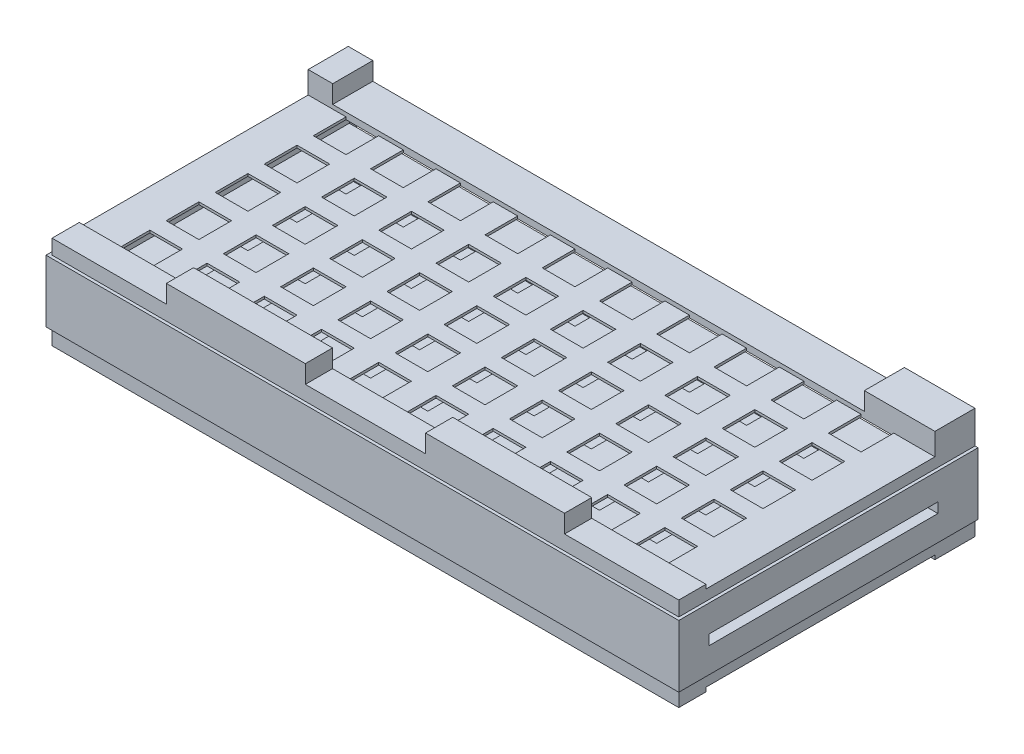
SolidWorks part; units mm, degrees
material "ABS"
ref_plane "Płaszczyzna przednia" through (0, 0, 0) normal (0, 0, 1) x (1, 0, 0)
ref_plane "Płaszczyzna górna" through (0, 0, 0) normal (0, 1, 0) x (1, 0, 0)
ref_plane "Płaszczyzna prawa" through (0, 0, 0) normal (1, 0, 0) x (0, 0, -1)
sketch "Szkic1" plane through (0, 0, 0) normal (0, 0, 1) x (1, 0, 0)
  line L15 (186, 34.1) -> (-188, 34.1)
  line L16 (186, 34.1) -> (186, -18.9)
  line L17 (186, -18.9) -> (-188, -18.9)
  line L18 (-188, 34.1) -> (-188, -18.9)
  point P0 (0, 0)
  dimension "D3" = 374
  dimension "D6" = 53
extrude "Dodanie-wyciągnięcie1" add sketch "Szkic1" along normal blind 177 contours L17 L18 L15 L16
sketch "Szkic5" plane through (0, -18.9, 0) normal (0, -1, 0) x (1, 0, 0)
  line L0 (186, 0) -> (-188, 0) construction
  line L1 (165.5, 48.5) -> (145.5, 48.5)
  line L2 (186, 177) -> (186, 0) construction
  line L3 (165.5, 48.5) -> (165.5, 68.5)
  line L4 (165.5, 68.5) -> (145.5, 68.5)
  line L5 (165.5, 18.5) -> (145.5, 18.5)
  line L6 (165.5, 18.5) -> (165.5, 38.5)
  line L7 (165.5, 38.5) -> (145.5, 38.5)
  line L8 (145.5, 18.5) -> (145.5, 38.5)
  line L9 (145.5, 48.5) -> (145.5, 68.5)
  line L10 (165.5, 78.5) -> (145.5, 78.5)
  line L11 (165.5, 78.5) -> (165.5, 98.5)
  line L12 (165.5, 98.5) -> (145.5, 98.5)
  line L13 (145.5, 78.5) -> (145.5, 98.5)
  line L14 (165.5, 108.5) -> (145.5, 108.5)
  line L15 (165.5, 108.5) -> (165.5, 128.5)
  line L16 (165.5, 128.5) -> (145.5, 128.5)
  line L17 (145.5, 108.5) -> (145.5, 128.5)
  line L18 (165.5, 138.5) -> (145.5, 138.5)
  line L19 (165.5, 138.5) -> (165.5, 158.5)
  line L20 (165.5, 158.5) -> (145.5, 158.5)
  line L21 (145.5, 138.5) -> (145.5, 158.5)
  line L22 (130.5, 48.5) -> (110.5, 48.5)
  line L23 (130.5, 48.5) -> (130.5, 68.5)
  line L24 (130.5, 68.5) -> (110.5, 68.5)
  line L25 (130.5, 18.5) -> (110.5, 18.5)
  line L26 (130.5, 18.5) -> (130.5, 38.5)
  line L27 (130.5, 38.5) -> (110.5, 38.5)
  line L28 (110.5, 18.5) -> (110.5, 38.5)
  line L29 (110.5, 48.5) -> (110.5, 68.5)
  line L30 (130.5, 78.5) -> (110.5, 78.5)
  line L31 (130.5, 78.5) -> (130.5, 98.5)
  line L32 (130.5, 98.5) -> (110.5, 98.5)
  line L33 (110.5, 78.5) -> (110.5, 98.5)
  line L34 (130.5, 108.5) -> (110.5, 108.5)
  line L35 (130.5, 108.5) -> (130.5, 128.5)
  line L36 (130.5, 128.5) -> (110.5, 128.5)
  line L37 (110.5, 108.5) -> (110.5, 128.5)
  line L38 (130.5, 138.5) -> (110.5, 138.5)
  line L39 (130.5, 138.5) -> (130.5, 158.5)
  line L40 (130.5, 158.5) -> (110.5, 158.5)
  line L41 (110.5, 138.5) -> (110.5, 158.5)
  line L42 (95.5, 48.5) -> (75.5, 48.5)
  line L43 (95.5, 48.5) -> (95.5, 68.5)
  line L44 (95.5, 68.5) -> (75.5, 68.5)
  line L45 (95.5, 18.5) -> (75.5, 18.5)
  line L46 (95.5, 18.5) -> (95.5, 38.5)
  line L47 (95.5, 38.5) -> (75.5, 38.5)
  line L48 (75.5, 18.5) -> (75.5, 38.5)
  line L49 (75.5, 48.5) -> (75.5, 68.5)
  line L50 (95.5, 78.5) -> (75.5, 78.5)
  line L51 (95.5, 78.5) -> (95.5, 98.5)
  line L52 (95.5, 98.5) -> (75.5, 98.5)
  line L53 (75.5, 78.5) -> (75.5, 98.5)
  line L54 (95.5, 108.5) -> (75.5, 108.5)
  line L55 (95.5, 108.5) -> (95.5, 128.5)
  line L56 (95.5, 128.5) -> (75.5, 128.5)
  line L57 (75.5, 108.5) -> (75.5, 128.5)
  line L58 (95.5, 138.5) -> (75.5, 138.5)
  line L59 (95.5, 138.5) -> (95.5, 158.5)
  line L60 (95.5, 158.5) -> (75.5, 158.5)
  line L61 (75.5, 138.5) -> (75.5, 158.5)
  line L62 (60.5, 48.5) -> (40.5, 48.5)
  line L63 (60.5, 48.5) -> (60.5, 68.5)
  line L64 (60.5, 68.5) -> (40.5, 68.5)
  line L65 (60.5, 18.5) -> (40.5, 18.5)
  line L66 (60.5, 18.5) -> (60.5, 38.5)
  line L67 (60.5, 38.5) -> (40.5, 38.5)
  line L68 (40.5, 18.5) -> (40.5, 38.5)
  line L69 (40.5, 48.5) -> (40.5, 68.5)
  line L70 (60.5, 78.5) -> (40.5, 78.5)
  line L71 (60.5, 78.5) -> (60.5, 98.5)
  line L72 (60.5, 98.5) -> (40.5, 98.5)
  line L73 (40.5, 78.5) -> (40.5, 98.5)
  line L74 (60.5, 108.5) -> (40.5, 108.5)
  line L75 (60.5, 108.5) -> (60.5, 128.5)
  line L76 (60.5, 128.5) -> (40.5, 128.5)
  line L77 (40.5, 108.5) -> (40.5, 128.5)
  line L78 (60.5, 138.5) -> (40.5, 138.5)
  line L79 (60.5, 138.5) -> (60.5, 158.5)
  line L80 (60.5, 158.5) -> (40.5, 158.5)
  line L81 (40.5, 138.5) -> (40.5, 158.5)
  line L82 (25.5, 48.5) -> (5.5, 48.5)
  line L83 (25.5, 48.5) -> (25.5, 68.5)
  line L84 (25.5, 68.5) -> (5.5, 68.5)
  line L85 (25.5, 18.5) -> (5.5, 18.5)
  line L86 (25.5, 18.5) -> (25.5, 38.5)
  line L87 (25.5, 38.5) -> (5.5, 38.5)
  line L88 (5.5, 18.5) -> (5.5, 38.5)
  line L89 (5.5, 48.5) -> (5.5, 68.5)
  line L90 (25.5, 78.5) -> (5.5, 78.5)
  line L91 (25.5, 78.5) -> (25.5, 98.5)
  line L92 (25.5, 98.5) -> (5.5, 98.5)
  line L93 (5.5, 78.5) -> (5.5, 98.5)
  line L94 (25.5, 108.5) -> (5.5, 108.5)
  line L95 (25.5, 108.5) -> (25.5, 128.5)
  line L96 (25.5, 128.5) -> (5.5, 128.5)
  line L97 (5.5, 108.5) -> (5.5, 128.5)
  line L98 (25.5, 138.5) -> (5.5, 138.5)
  line L99 (25.5, 138.5) -> (25.5, 158.5)
  line L100 (25.5, 158.5) -> (5.5, 158.5)
  line L101 (5.5, 138.5) -> (5.5, 158.5)
  line L102 (-9.5, 48.5) -> (-29.5, 48.5)
  line L103 (-9.5, 48.5) -> (-9.5, 68.5)
  line L104 (-9.5, 68.5) -> (-29.5, 68.5)
  line L105 (-9.5, 18.5) -> (-29.5, 18.5)
  line L106 (-9.5, 18.5) -> (-9.5, 38.5)
  line L107 (-9.5, 38.5) -> (-29.5, 38.5)
  line L108 (-29.5, 18.5) -> (-29.5, 38.5)
  line L109 (-29.5, 48.5) -> (-29.5, 68.5)
  line L110 (-9.5, 78.5) -> (-29.5, 78.5)
  line L111 (-9.5, 78.5) -> (-9.5, 98.5)
  line L112 (-9.5, 98.5) -> (-29.5, 98.5)
  line L113 (-29.5, 78.5) -> (-29.5, 98.5)
  line L114 (-9.5, 108.5) -> (-29.5, 108.5)
  line L115 (-9.5, 108.5) -> (-9.5, 128.5)
  line L116 (-9.5, 128.5) -> (-29.5, 128.5)
  line L117 (-29.5, 108.5) -> (-29.5, 128.5)
  line L118 (-9.5, 138.5) -> (-29.5, 138.5)
  line L119 (-9.5, 138.5) -> (-9.5, 158.5)
  line L120 (-9.5, 158.5) -> (-29.5, 158.5)
  line L121 (-29.5, 138.5) -> (-29.5, 158.5)
  line L122 (-44.5, 48.5) -> (-64.5, 48.5)
  line L123 (-44.5, 48.5) -> (-44.5, 68.5)
  line L124 (-44.5, 68.5) -> (-64.5, 68.5)
  line L125 (-44.5, 18.5) -> (-64.5, 18.5)
  line L126 (-44.5, 18.5) -> (-44.5, 38.5)
  line L127 (-44.5, 38.5) -> (-64.5, 38.5)
  line L128 (-64.5, 18.5) -> (-64.5, 38.5)
  line L129 (-64.5, 48.5) -> (-64.5, 68.5)
  line L130 (-44.5, 78.5) -> (-64.5, 78.5)
  line L131 (-44.5, 78.5) -> (-44.5, 98.5)
  line L132 (-44.5, 98.5) -> (-64.5, 98.5)
  line L133 (-64.5, 78.5) -> (-64.5, 98.5)
  line L134 (-44.5, 108.5) -> (-64.5, 108.5)
  line L135 (-44.5, 108.5) -> (-44.5, 128.5)
  line L136 (-44.5, 128.5) -> (-64.5, 128.5)
  line L137 (-64.5, 108.5) -> (-64.5, 128.5)
  line L138 (-44.5, 138.5) -> (-64.5, 138.5)
  line L139 (-44.5, 138.5) -> (-44.5, 158.5)
  line L140 (-44.5, 158.5) -> (-64.5, 158.5)
  line L141 (-64.5, 138.5) -> (-64.5, 158.5)
  line L142 (-79.5, 48.5) -> (-99.5, 48.5)
  line L143 (-79.5, 48.5) -> (-79.5, 68.5)
  line L144 (-79.5, 68.5) -> (-99.5, 68.5)
  line L145 (-79.5, 18.5) -> (-99.5, 18.5)
  line L146 (-79.5, 18.5) -> (-79.5, 38.5)
  line L147 (-79.5, 38.5) -> (-99.5, 38.5)
  line L148 (-99.5, 18.5) -> (-99.5, 38.5)
  line L149 (-99.5, 48.5) -> (-99.5, 68.5)
  line L150 (-79.5, 78.5) -> (-99.5, 78.5)
  line L151 (-79.5, 78.5) -> (-79.5, 98.5)
  line L152 (-79.5, 98.5) -> (-99.5, 98.5)
  line L153 (-99.5, 78.5) -> (-99.5, 98.5)
  line L154 (-79.5, 108.5) -> (-99.5, 108.5)
  line L155 (-79.5, 108.5) -> (-79.5, 128.5)
  line L156 (-79.5, 128.5) -> (-99.5, 128.5)
  line L157 (-99.5, 108.5) -> (-99.5, 128.5)
  line L158 (-79.5, 138.5) -> (-99.5, 138.5)
  line L159 (-79.5, 138.5) -> (-79.5, 158.5)
  line L160 (-79.5, 158.5) -> (-99.5, 158.5)
  line L161 (-99.5, 138.5) -> (-99.5, 158.5)
  line L162 (-114.5, 48.5) -> (-134.5, 48.5)
  line L163 (-114.5, 48.5) -> (-114.5, 68.5)
  line L164 (-114.5, 68.5) -> (-134.5, 68.5)
  line L165 (-114.5, 18.5) -> (-134.5, 18.5)
  line L166 (-114.5, 18.5) -> (-114.5, 38.5)
  line L167 (-114.5, 38.5) -> (-134.5, 38.5)
  line L168 (-134.5, 18.5) -> (-134.5, 38.5)
  line L169 (-134.5, 48.5) -> (-134.5, 68.5)
  line L170 (-114.5, 78.5) -> (-134.5, 78.5)
  line L171 (-114.5, 78.5) -> (-114.5, 98.5)
  line L172 (-114.5, 98.5) -> (-134.5, 98.5)
  line L173 (-134.5, 78.5) -> (-134.5, 98.5)
  line L174 (-114.5, 108.5) -> (-134.5, 108.5)
  line L175 (-114.5, 108.5) -> (-114.5, 128.5)
  line L176 (-114.5, 128.5) -> (-134.5, 128.5)
  line L177 (-134.5, 108.5) -> (-134.5, 128.5)
  line L178 (-114.5, 138.5) -> (-134.5, 138.5)
  line L179 (-114.5, 138.5) -> (-114.5, 158.5)
  line L180 (-114.5, 158.5) -> (-134.5, 158.5)
  line L181 (-134.5, 138.5) -> (-134.5, 158.5)
  line L182 (-149.5, 48.5) -> (-169.5, 48.5)
  line L183 (-149.5, 48.5) -> (-149.5, 68.5)
  line L184 (-149.5, 68.5) -> (-169.5, 68.5)
  line L185 (-149.5, 18.5) -> (-169.5, 18.5)
  line L186 (-149.5, 18.5) -> (-149.5, 38.5)
  line L187 (-149.5, 38.5) -> (-169.5, 38.5)
  line L188 (-169.5, 18.5) -> (-169.5, 38.5)
  line L189 (-169.5, 48.5) -> (-169.5, 68.5)
  line L190 (-149.5, 78.5) -> (-169.5, 78.5)
  line L191 (-149.5, 78.5) -> (-149.5, 98.5)
  line L192 (-149.5, 98.5) -> (-169.5, 98.5)
  line L193 (-169.5, 78.5) -> (-169.5, 98.5)
  line L194 (-149.5, 108.5) -> (-169.5, 108.5)
  line L195 (-149.5, 108.5) -> (-149.5, 128.5)
  line L196 (-149.5, 128.5) -> (-169.5, 128.5)
  line L197 (-169.5, 108.5) -> (-169.5, 128.5)
  line L198 (-149.5, 138.5) -> (-169.5, 138.5)
  line L199 (-149.5, 138.5) -> (-149.5, 158.5)
  line L200 (-149.5, 158.5) -> (-169.5, 158.5)
  line L201 (-169.5, 138.5) -> (-169.5, 158.5)
  line L202 (186, 177) -> (-188, 177) construction
  line L203 (-188, 177) -> (-188, 0) construction
  dimension "D1" = 18.5
  dimension "D2" = 20.5
  dimension "D3" = 20
  dimension "D4" = 20
  dimension "D7" = 20
  dimension "D8" = 20
  dimension "D9" = 15
  dimension "D10" = 18.5
  dimension "D11" = 18.5
  dimension "D5" = 5
  dimension "D6" = 10
extrude "Wytnij-wyciągnięcie4" cut sketch "Szkic5" against normal blind 104
sketch "Szkic7" plane through (0, 0, 0) normal (0, 0, -1) x (-1, 0, 0)
  line L5 (-186, -18.9) -> (188, -18.9) construction
  line L7 (-184, 32.1) -> (186, 32.1)
  line L8 (-184, 32.1) -> (-184, 12.7)
  line L9 (-184, 12.7) -> (186, 12.7)
  line L10 (186, 32.1) -> (186, 12.7)
  line L12 (-186, 34.1) -> (-186, -18.9) construction
  line L13 (-184, -16.9) -> (186, -16.9)
  line L14 (-184, -16.9) -> (-184, 2.5)
  line L15 (-184, 2.5) -> (186, 2.5)
  line L16 (186, -16.9) -> (186, 2.5)
  line L17 (-186, 34.1) -> (188, 34.1) construction
  dimension "D1" = 370
  dimension "D2" = 2
  dimension "D3" = 2
  dimension "D4" = 2
  dimension "D5" = 2
  dimension "D6" = 370
  dimension "D7" = 370
  dimension "D8" = 19.4
  dimension "D9" = 19.4
extrude "Wytnij-wyciągnięcie5" cut sketch "Szkic7" against normal blind 175
sketch "Szkic9" plane through (186, 0, 0) normal (1, 0, 0) x (0, 0, -1)
  line L15 (-158.5, 10.7) -> (-158.5, 4.5)
  line L17 (-18.5, 10.7) -> (-158.5, 10.7)
  line L18 (-18.5, 10.7) -> (-18.5, 4.5)
  line L19 (-18.5, 4.5) -> (-158.5, 4.5)
extrude "Wytnij-wyciągnięcie6" cut sketch "Szkic9" against normal blind 374
sketch "Szkic15" plane through (0, 34.1, 0) normal (0, 1, 0) x (1, 0, 0)
  line L1 (-188, 0) -> (186, 0)
  line L2 (-188, 0) -> (-188, -177)
  line L3 (-188, -177) -> (186, -177)
  line L4 (186, 0) -> (186, -177)
  line L5 (-169.5, -18.5) -> (-149.5, -18.5)
  line L6 (-169.5, -18.5) -> (-169.5, -38.5)
  line L7 (-169.5, -38.5) -> (-149.5, -38.5)
  line L8 (-149.5, -18.5) -> (-149.5, -38.5)
  line L9 (-134.5, -18.5) -> (-114.5, -18.5)
  line L10 (-134.5, -18.5) -> (-134.5, -38.5)
  line L11 (-134.5, -38.5) -> (-114.5, -38.5)
  line L12 (-114.5, -18.5) -> (-114.5, -38.5)
  line L13 (-99.5, -18.5) -> (-79.5, -18.5)
  line L14 (-99.5, -18.5) -> (-99.5, -38.5)
  line L15 (-99.5, -38.5) -> (-79.5, -38.5)
  line L16 (-79.5, -18.5) -> (-79.5, -38.5)
  line L17 (-64.5, -18.5) -> (-44.5, -18.5)
  line L18 (-64.5, -18.5) -> (-64.5, -38.5)
  line L19 (-64.5, -38.5) -> (-44.5, -38.5)
  line L20 (-44.5, -18.5) -> (-44.5, -38.5)
  line L21 (-29.5, -18.5) -> (-9.5, -18.5)
  line L22 (-29.5, -18.5) -> (-29.5, -38.5)
  line L23 (-29.5, -38.5) -> (-9.5, -38.5)
  line L24 (-9.5, -18.5) -> (-9.5, -38.5)
  line L25 (5.5, -18.5) -> (25.5, -18.5)
  line L26 (5.5, -18.5) -> (5.5, -38.5)
  line L27 (5.5, -38.5) -> (25.5, -38.5)
  line L28 (25.5, -18.5) -> (25.5, -38.5)
  line L29 (40.5, -18.5) -> (60.5, -18.5)
  line L30 (40.5, -18.5) -> (40.5, -38.5)
  line L31 (40.5, -38.5) -> (60.5, -38.5)
  line L32 (60.5, -18.5) -> (60.5, -38.5)
  line L33 (75.5, -18.5) -> (95.5, -18.5)
  line L34 (75.5, -18.5) -> (75.5, -38.5)
  line L35 (75.5, -38.5) -> (95.5, -38.5)
  line L36 (95.5, -18.5) -> (95.5, -38.5)
  line L37 (110.5, -18.5) -> (130.5, -18.5)
  line L38 (110.5, -18.5) -> (110.5, -38.5)
  line L39 (110.5, -38.5) -> (130.5, -38.5)
  line L40 (130.5, -18.5) -> (130.5, -38.5)
  line L41 (145.5, -18.5) -> (165.5, -18.5)
  line L42 (145.5, -18.5) -> (145.5, -38.5)
  line L43 (145.5, -38.5) -> (165.5, -38.5)
  line L44 (165.5, -18.5) -> (165.5, -38.5)
  line L45 (145.5, -48.5) -> (165.5, -48.5)
  line L46 (145.5, -48.5) -> (145.5, -68.5)
  line L47 (145.5, -68.5) -> (165.5, -68.5)
  line L48 (165.5, -48.5) -> (165.5, -68.5)
  line L49 (145.5, -78.5) -> (165.5, -78.5)
  line L50 (145.5, -78.5) -> (145.5, -98.5)
  line L51 (145.5, -98.5) -> (165.5, -98.5)
  line L52 (165.5, -78.5) -> (165.5, -98.5)
  line L53 (145.5, -108.5) -> (165.5, -108.5)
  line L54 (145.5, -108.5) -> (145.5, -128.5)
  line L55 (145.5, -128.5) -> (165.5, -128.5)
  line L56 (165.5, -108.5) -> (165.5, -128.5)
  line L57 (145.5, -138.5) -> (165.5, -138.5)
  line L58 (145.5, -138.5) -> (145.5, -158.5)
  line L59 (145.5, -158.5) -> (165.5, -158.5)
  line L60 (165.5, -138.5) -> (165.5, -158.5)
  line L61 (110.5, -48.5) -> (130.5, -48.5)
  line L62 (110.5, -48.5) -> (110.5, -68.5)
  line L63 (110.5, -68.5) -> (130.5, -68.5)
  line L64 (130.5, -48.5) -> (130.5, -68.5)
  line L65 (110.5, -78.5) -> (130.5, -78.5)
  line L66 (110.5, -78.5) -> (110.5, -98.5)
  line L67 (110.5, -98.5) -> (130.5, -98.5)
  line L68 (130.5, -78.5) -> (130.5, -98.5)
  line L69 (110.5, -108.5) -> (130.5, -108.5)
  line L70 (110.5, -108.5) -> (110.5, -128.5)
  line L71 (110.5, -128.5) -> (130.5, -128.5)
  line L72 (130.5, -108.5) -> (130.5, -128.5)
  line L73 (110.5, -138.5) -> (130.5, -138.5)
  line L74 (110.5, -138.5) -> (110.5, -158.5)
  line L75 (110.5, -158.5) -> (130.5, -158.5)
  line L76 (130.5, -138.5) -> (130.5, -158.5)
  line L77 (75.5, -48.5) -> (95.5, -48.5)
  line L78 (75.5, -48.5) -> (75.5, -68.5)
  line L79 (75.5, -68.5) -> (95.5, -68.5)
  line L80 (95.5, -48.5) -> (95.5, -68.5)
  line L81 (75.5, -78.5) -> (95.5, -78.5)
  line L82 (75.5, -78.5) -> (75.5, -98.5)
  line L83 (75.5, -98.5) -> (95.5, -98.5)
  line L84 (95.5, -78.5) -> (95.5, -98.5)
  line L85 (75.5, -108.5) -> (95.5, -108.5)
  line L86 (75.5, -108.5) -> (75.5, -128.5)
  line L87 (75.5, -128.5) -> (95.5, -128.5)
  line L88 (95.5, -108.5) -> (95.5, -128.5)
  line L89 (75.5, -138.5) -> (95.5, -138.5)
  line L90 (75.5, -138.5) -> (75.5, -158.5)
  line L91 (75.5, -158.5) -> (95.5, -158.5)
  line L92 (95.5, -138.5) -> (95.5, -158.5)
  line L93 (40.5, -48.5) -> (60.5, -48.5)
  line L94 (40.5, -48.5) -> (40.5, -68.5)
  line L95 (40.5, -68.5) -> (60.5, -68.5)
  line L96 (60.5, -48.5) -> (60.5, -68.5)
  line L97 (40.5, -78.5) -> (60.5, -78.5)
  line L98 (40.5, -78.5) -> (40.5, -98.5)
  line L99 (40.5, -98.5) -> (60.5, -98.5)
  line L100 (60.5, -78.5) -> (60.5, -98.5)
  line L101 (40.5, -108.5) -> (60.5, -108.5)
  line L102 (40.5, -108.5) -> (40.5, -128.5)
  line L103 (40.5, -128.5) -> (60.5, -128.5)
  line L104 (60.5, -108.5) -> (60.5, -128.5)
  line L105 (5.5, -48.5) -> (25.5, -48.5)
  line L106 (5.5, -48.5) -> (5.5, -68.5)
  line L107 (5.5, -68.5) -> (25.5, -68.5)
  line L108 (25.5, -48.5) -> (25.5, -68.5)
  line L109 (5.5, -78.5) -> (25.5, -78.5)
  line L110 (5.5, -78.5) -> (5.5, -98.5)
  line L111 (5.5, -98.5) -> (25.5, -98.5)
  line L112 (25.5, -78.5) -> (25.5, -98.5)
  line L113 (5.5, -108.5) -> (25.5, -108.5)
  line L114 (5.5, -108.5) -> (5.5, -128.5)
  line L115 (5.5, -128.5) -> (25.5, -128.5)
  line L116 (25.5, -108.5) -> (25.5, -128.5)
  line L117 (5.5, -138.5) -> (25.5, -138.5)
  line L118 (5.5, -138.5) -> (5.5, -158.5)
  line L119 (5.5, -158.5) -> (25.5, -158.5)
  line L120 (25.5, -138.5) -> (25.5, -158.5)
  line L121 (40.5, -138.5) -> (60.5, -138.5)
  line L122 (40.5, -138.5) -> (40.5, -158.5)
  line L123 (40.5, -158.5) -> (60.5, -158.5)
  line L124 (60.5, -138.5) -> (60.5, -158.5)
  line L125 (-29.5, -48.5) -> (-9.5, -48.5)
  line L126 (-29.5, -48.5) -> (-29.5, -68.5)
  line L127 (-29.5, -68.5) -> (-9.5, -68.5)
  line L128 (-9.5, -48.5) -> (-9.5, -68.5)
  line L129 (-29.5, -78.5) -> (-9.5, -78.5)
  line L130 (-29.5, -78.5) -> (-29.5, -98.5)
  line L131 (-29.5, -98.5) -> (-9.5, -98.5)
  line L132 (-9.5, -78.5) -> (-9.5, -98.5)
  line L133 (-29.5, -108.5) -> (-9.5, -108.5)
  line L134 (-29.5, -108.5) -> (-29.5, -128.5)
  line L135 (-29.5, -128.5) -> (-9.5, -128.5)
  line L136 (-9.5, -108.5) -> (-9.5, -128.5)
  line L137 (-29.5, -138.5) -> (-9.5, -138.5)
  line L138 (-29.5, -138.5) -> (-29.5, -158.5)
  line L139 (-29.5, -158.5) -> (-9.5, -158.5)
  line L140 (-9.5, -138.5) -> (-9.5, -158.5)
  line L141 (-64.5, -48.5) -> (-44.5, -48.5)
  line L142 (-64.5, -48.5) -> (-64.5, -68.5)
  line L143 (-64.5, -68.5) -> (-44.5, -68.5)
  line L144 (-44.5, -48.5) -> (-44.5, -68.5)
  line L145 (-64.5, -78.5) -> (-44.5, -78.5)
  line L146 (-64.5, -78.5) -> (-64.5, -98.5)
  line L147 (-64.5, -98.5) -> (-44.5, -98.5)
  line L148 (-44.5, -78.5) -> (-44.5, -98.5)
  line L149 (-64.5, -108.5) -> (-44.5, -108.5)
  line L150 (-64.5, -108.5) -> (-64.5, -128.5)
  line L151 (-64.5, -128.5) -> (-44.5, -128.5)
  line L152 (-44.5, -108.5) -> (-44.5, -128.5)
  line L153 (-64.5, -138.5) -> (-44.5, -138.5)
  line L154 (-64.5, -138.5) -> (-64.5, -158.5)
  line L155 (-64.5, -158.5) -> (-44.5, -158.5)
  line L156 (-44.5, -138.5) -> (-44.5, -158.5)
  line L157 (-99.5, -48.5) -> (-79.5, -48.5)
  line L158 (-99.5, -48.5) -> (-99.5, -68.5)
  line L159 (-99.5, -68.5) -> (-79.5, -68.5)
  line L160 (-79.5, -48.5) -> (-79.5, -68.5)
  line L161 (-99.5, -78.5) -> (-79.5, -78.5)
  line L162 (-99.5, -78.5) -> (-99.5, -98.5)
  line L163 (-99.5, -98.5) -> (-79.5, -98.5)
  line L164 (-79.5, -78.5) -> (-79.5, -98.5)
  line L165 (-99.5, -108.5) -> (-79.5, -108.5)
  line L166 (-99.5, -108.5) -> (-99.5, -128.5)
  line L167 (-99.5, -128.5) -> (-79.5, -128.5)
  line L168 (-79.5, -108.5) -> (-79.5, -128.5)
  line L169 (-99.5, -138.5) -> (-79.5, -138.5)
  line L170 (-99.5, -138.5) -> (-99.5, -158.5)
  line L171 (-99.5, -158.5) -> (-79.5, -158.5)
  line L172 (-79.5, -138.5) -> (-79.5, -158.5)
  line L173 (-134.5, -48.5) -> (-114.5, -48.5)
  line L174 (-134.5, -48.5) -> (-134.5, -68.5)
  line L175 (-134.5, -68.5) -> (-114.5, -68.5)
  line L176 (-114.5, -48.5) -> (-114.5, -68.5)
  line L177 (-134.5, -78.5) -> (-114.5, -78.5)
  line L178 (-134.5, -78.5) -> (-134.5, -98.5)
  line L179 (-134.5, -98.5) -> (-114.5, -98.5)
  line L180 (-114.5, -78.5) -> (-114.5, -98.5)
  line L181 (-134.5, -108.5) -> (-114.5, -108.5)
  line L182 (-134.5, -108.5) -> (-134.5, -128.5)
  line L183 (-134.5, -128.5) -> (-114.5, -128.5)
  line L184 (-114.5, -108.5) -> (-114.5, -128.5)
  line L185 (-134.5, -138.5) -> (-114.5, -138.5)
  line L186 (-134.5, -138.5) -> (-134.5, -158.5)
  line L187 (-134.5, -158.5) -> (-114.5, -158.5)
  line L188 (-114.5, -138.5) -> (-114.5, -158.5)
  line L189 (-169.5, -48.5) -> (-149.5, -48.5)
  line L190 (-169.5, -48.5) -> (-169.5, -68.5)
  line L191 (-169.5, -68.5) -> (-149.5, -68.5)
  line L192 (-149.5, -48.5) -> (-149.5, -68.5)
  line L193 (-169.5, -78.5) -> (-149.5, -78.5)
  line L194 (-169.5, -78.5) -> (-169.5, -98.5)
  line L195 (-169.5, -98.5) -> (-149.5, -98.5)
  line L196 (-149.5, -78.5) -> (-149.5, -98.5)
  line L197 (-169.5, -108.5) -> (-149.5, -108.5)
  line L198 (-169.5, -108.5) -> (-169.5, -128.5)
  line L199 (-169.5, -128.5) -> (-149.5, -128.5)
  line L200 (-149.5, -108.5) -> (-149.5, -128.5)
  line L201 (-169.5, -138.5) -> (-149.5, -138.5)
  line L202 (-169.5, -138.5) -> (-169.5, -158.5)
  line L203 (-169.5, -158.5) -> (-149.5, -158.5)
  line L204 (-149.5, -138.5) -> (-149.5, -158.5)
extrude "Dodanie-wyciągnięcie6" add sketch "Szkic15" along normal blind 1
sketch "Szkic16" plane through (0, -18.9, 0) normal (0, -1, 0) x (1, 0, 0)
  line L1 (186, 0) -> (-188, 0)
  line L2 (186, 0) -> (186, 177)
  line L3 (186, 177) -> (-188, 177)
  line L4 (-188, 0) -> (-188, 177)
  line L5 (165.5, 18.5) -> (145.5, 18.5)
  line L6 (165.5, 18.5) -> (165.5, 38.5)
  line L7 (165.5, 38.5) -> (145.5, 38.5)
  line L8 (145.5, 18.5) -> (145.5, 38.5)
  line L9 (130.5, 18.5) -> (110.5, 18.5)
  line L10 (130.5, 18.5) -> (130.5, 38.5)
  line L11 (130.5, 38.5) -> (110.5, 38.5)
  line L12 (110.5, 18.5) -> (110.5, 38.5)
  line L13 (95.5, 18.5) -> (75.5, 18.5)
  line L14 (95.5, 18.5) -> (95.5, 38.5)
  line L15 (95.5, 38.5) -> (75.5, 38.5)
  line L16 (75.5, 18.5) -> (75.5, 38.5)
  line L17 (60.5, 18.5) -> (40.5, 18.5)
  line L18 (60.5, 18.5) -> (60.5, 38.5)
  line L19 (60.5, 38.5) -> (40.5, 38.5)
  line L20 (40.5, 18.5) -> (40.5, 38.5)
  line L21 (25.5, 18.5) -> (5.5, 18.5)
  line L22 (25.5, 18.5) -> (25.5, 38.5)
  line L23 (25.5, 38.5) -> (5.5, 38.5)
  line L24 (5.5, 18.5) -> (5.5, 38.5)
  line L25 (-9.5, 18.5) -> (-29.5, 18.5)
  line L26 (-9.5, 18.5) -> (-9.5, 38.5)
  line L27 (-9.5, 38.5) -> (-29.5, 38.5)
  line L28 (-29.5, 18.5) -> (-29.5, 38.5)
  line L29 (-44.5, 18.5) -> (-64.5, 18.5)
  line L30 (-44.5, 18.5) -> (-44.5, 38.5)
  line L31 (-44.5, 38.5) -> (-64.5, 38.5)
  line L32 (-64.5, 18.5) -> (-64.5, 38.5)
  line L33 (-79.5, 18.5) -> (-99.5, 18.5)
  line L34 (-79.5, 18.5) -> (-79.5, 38.5)
  line L35 (-79.5, 38.5) -> (-99.5, 38.5)
  line L36 (-99.5, 18.5) -> (-99.5, 38.5)
  line L37 (-114.5, 18.5) -> (-134.5, 18.5)
  line L38 (-114.5, 18.5) -> (-114.5, 38.5)
  line L39 (-114.5, 38.5) -> (-134.5, 38.5)
  line L40 (-134.5, 18.5) -> (-134.5, 38.5)
  line L41 (-149.5, 18.5) -> (-169.5, 18.5)
  line L42 (-149.5, 18.5) -> (-149.5, 38.5)
  line L43 (-149.5, 38.5) -> (-169.5, 38.5)
  line L44 (-169.5, 18.5) -> (-169.5, 38.5)
  line L45 (165.5, 48.5) -> (145.5, 48.5)
  line L46 (165.5, 48.5) -> (165.5, 68.5)
  line L47 (165.5, 68.5) -> (145.5, 68.5)
  line L48 (145.5, 48.5) -> (145.5, 68.5)
  line L49 (130.5, 48.5) -> (110.5, 48.5)
  line L50 (130.5, 48.5) -> (130.5, 68.5)
  line L51 (130.5, 68.5) -> (110.5, 68.5)
  line L52 (110.5, 48.5) -> (110.5, 68.5)
  line L53 (95.5, 48.5) -> (75.5, 48.5)
  line L54 (95.5, 48.5) -> (95.5, 68.5)
  line L55 (95.5, 68.5) -> (75.5, 68.5)
  line L56 (75.5, 48.5) -> (75.5, 68.5)
  line L57 (60.5, 48.5) -> (40.5, 48.5)
  line L58 (60.5, 48.5) -> (60.5, 68.5)
  line L59 (60.5, 68.5) -> (40.5, 68.5)
  line L60 (40.5, 48.5) -> (40.5, 68.5)
  line L61 (25.5, 48.5) -> (5.5, 48.5)
  line L62 (25.5, 48.5) -> (25.5, 68.5)
  line L63 (25.5, 68.5) -> (5.5, 68.5)
  line L64 (5.5, 48.5) -> (5.5, 68.5)
  line L65 (-9.5, 48.5) -> (-29.5, 48.5)
  line L66 (-9.5, 48.5) -> (-9.5, 68.5)
  line L67 (-9.5, 68.5) -> (-29.5, 68.5)
  line L68 (-29.5, 48.5) -> (-29.5, 68.5)
  line L69 (-44.5, 48.5) -> (-64.5, 48.5)
  line L70 (-44.5, 48.5) -> (-44.5, 68.5)
  line L71 (-44.5, 68.5) -> (-64.5, 68.5)
  line L72 (-64.5, 48.5) -> (-64.5, 68.5)
  line L73 (-79.5, 48.5) -> (-99.5, 48.5)
  line L74 (-79.5, 48.5) -> (-79.5, 68.5)
  line L75 (-79.5, 68.5) -> (-99.5, 68.5)
  line L76 (-99.5, 48.5) -> (-99.5, 68.5)
  line L77 (-114.5, 48.5) -> (-134.5, 48.5)
  line L78 (-114.5, 48.5) -> (-114.5, 68.5)
  line L79 (-114.5, 68.5) -> (-134.5, 68.5)
  line L80 (-134.5, 48.5) -> (-134.5, 68.5)
  line L81 (-149.5, 48.5) -> (-169.5, 48.5)
  line L82 (-149.5, 48.5) -> (-149.5, 68.5)
  line L83 (-149.5, 68.5) -> (-169.5, 68.5)
  line L84 (-169.5, 48.5) -> (-169.5, 68.5)
  line L85 (-149.5, 78.5) -> (-169.5, 78.5)
  line L86 (-149.5, 78.5) -> (-149.5, 98.5)
  line L87 (-149.5, 98.5) -> (-169.5, 98.5)
  line L88 (-169.5, 78.5) -> (-169.5, 98.5)
  line L89 (-149.5, 108.5) -> (-169.5, 108.5)
  line L90 (-149.5, 108.5) -> (-149.5, 128.5)
  line L91 (-149.5, 128.5) -> (-169.5, 128.5)
  line L92 (-169.5, 108.5) -> (-169.5, 128.5)
  line L93 (-149.5, 138.5) -> (-169.5, 138.5)
  line L94 (-149.5, 138.5) -> (-149.5, 158.5)
  line L95 (-149.5, 158.5) -> (-169.5, 158.5)
  line L96 (-169.5, 138.5) -> (-169.5, 158.5)
  line L97 (-114.5, 78.5) -> (-134.5, 78.5)
  line L98 (-114.5, 78.5) -> (-114.5, 98.5)
  line L99 (-114.5, 98.5) -> (-134.5, 98.5)
  line L100 (-134.5, 78.5) -> (-134.5, 98.5)
  line L101 (-114.5, 108.5) -> (-134.5, 108.5)
  line L102 (-114.5, 108.5) -> (-114.5, 128.5)
  line L103 (-114.5, 128.5) -> (-134.5, 128.5)
  line L104 (-134.5, 108.5) -> (-134.5, 128.5)
  line L105 (-114.5, 138.5) -> (-134.5, 138.5)
  line L106 (-114.5, 138.5) -> (-114.5, 158.5)
  line L107 (-114.5, 158.5) -> (-134.5, 158.5)
  line L108 (-134.5, 138.5) -> (-134.5, 158.5)
  line L109 (-79.5, 78.5) -> (-99.5, 78.5)
  line L110 (-79.5, 78.5) -> (-79.5, 98.5)
  line L111 (-79.5, 98.5) -> (-99.5, 98.5)
  line L112 (-99.5, 78.5) -> (-99.5, 98.5)
  line L113 (-79.5, 108.5) -> (-99.5, 108.5)
  line L114 (-79.5, 108.5) -> (-79.5, 128.5)
  line L115 (-79.5, 128.5) -> (-99.5, 128.5)
  line L116 (-99.5, 108.5) -> (-99.5, 128.5)
  line L117 (-79.5, 138.5) -> (-99.5, 138.5)
  line L118 (-79.5, 138.5) -> (-79.5, 158.5)
  line L119 (-79.5, 158.5) -> (-99.5, 158.5)
  line L120 (-99.5, 138.5) -> (-99.5, 158.5)
  line L121 (-44.5, 78.5) -> (-64.5, 78.5)
  line L122 (-44.5, 78.5) -> (-44.5, 98.5)
  line L123 (-44.5, 98.5) -> (-64.5, 98.5)
  line L124 (-64.5, 78.5) -> (-64.5, 98.5)
  line L125 (-44.5, 108.5) -> (-64.5, 108.5)
  line L126 (-44.5, 108.5) -> (-44.5, 128.5)
  line L127 (-44.5, 128.5) -> (-64.5, 128.5)
  line L128 (-64.5, 108.5) -> (-64.5, 128.5)
  line L129 (-44.5, 138.5) -> (-64.5, 138.5)
  line L130 (-44.5, 138.5) -> (-44.5, 158.5)
  line L131 (-44.5, 158.5) -> (-64.5, 158.5)
  line L132 (-64.5, 138.5) -> (-64.5, 158.5)
  line L133 (-9.5, 78.5) -> (-29.5, 78.5)
  line L134 (-9.5, 78.5) -> (-9.5, 98.5)
  line L135 (-9.5, 98.5) -> (-29.5, 98.5)
  line L136 (-29.5, 78.5) -> (-29.5, 98.5)
  line L137 (-9.5, 108.5) -> (-29.5, 108.5)
  line L138 (-9.5, 108.5) -> (-9.5, 128.5)
  line L139 (-9.5, 128.5) -> (-29.5, 128.5)
  line L140 (-29.5, 108.5) -> (-29.5, 128.5)
  line L141 (-9.5, 138.5) -> (-29.5, 138.5)
  line L142 (-9.5, 138.5) -> (-9.5, 158.5)
  line L143 (-9.5, 158.5) -> (-29.5, 158.5)
  line L144 (-29.5, 138.5) -> (-29.5, 158.5)
  line L145 (25.5, 78.5) -> (5.5, 78.5)
  line L146 (25.5, 78.5) -> (25.5, 98.5)
  line L147 (25.5, 98.5) -> (5.5, 98.5)
  line L148 (5.5, 78.5) -> (5.5, 98.5)
  line L149 (25.5, 108.5) -> (5.5, 108.5)
  line L150 (25.5, 108.5) -> (25.5, 128.5)
  line L151 (25.5, 128.5) -> (5.5, 128.5)
  line L152 (5.5, 108.5) -> (5.5, 128.5)
  line L153 (25.5, 138.5) -> (5.5, 138.5)
  line L154 (25.5, 138.5) -> (25.5, 158.5)
  line L155 (25.5, 158.5) -> (5.5, 158.5)
  line L156 (5.5, 138.5) -> (5.5, 158.5)
  line L157 (60.5, 78.5) -> (40.5, 78.5)
  line L158 (60.5, 78.5) -> (60.5, 98.5)
  line L159 (60.5, 98.5) -> (40.5, 98.5)
  line L160 (40.5, 78.5) -> (40.5, 98.5)
  line L161 (60.5, 108.5) -> (40.5, 108.5)
  line L162 (60.5, 108.5) -> (60.5, 128.5)
  line L163 (60.5, 128.5) -> (40.5, 128.5)
  line L164 (40.5, 108.5) -> (40.5, 128.5)
  line L165 (60.5, 138.5) -> (40.5, 138.5)
  line L166 (60.5, 138.5) -> (60.5, 158.5)
  line L167 (60.5, 158.5) -> (40.5, 158.5)
  line L168 (40.5, 138.5) -> (40.5, 158.5)
  line L169 (95.5, 78.5) -> (75.5, 78.5)
  line L170 (95.5, 78.5) -> (95.5, 98.5)
  line L171 (95.5, 98.5) -> (75.5, 98.5)
  line L172 (75.5, 78.5) -> (75.5, 98.5)
  line L173 (95.5, 108.5) -> (75.5, 108.5)
  line L174 (95.5, 108.5) -> (95.5, 128.5)
  line L175 (95.5, 128.5) -> (75.5, 128.5)
  line L176 (75.5, 108.5) -> (75.5, 128.5)
  line L177 (95.5, 138.5) -> (75.5, 138.5)
  line L178 (95.5, 138.5) -> (95.5, 158.5)
  line L179 (95.5, 158.5) -> (75.5, 158.5)
  line L180 (75.5, 138.5) -> (75.5, 158.5)
  line L181 (130.5, 78.5) -> (110.5, 78.5)
  line L182 (130.5, 78.5) -> (130.5, 98.5)
  line L183 (130.5, 98.5) -> (110.5, 98.5)
  line L184 (110.5, 78.5) -> (110.5, 98.5)
  line L185 (165.5, 78.5) -> (145.5, 78.5)
  line L186 (165.5, 78.5) -> (165.5, 98.5)
  line L187 (165.5, 98.5) -> (145.5, 98.5)
  line L188 (145.5, 78.5) -> (145.5, 98.5)
  line L189 (165.5, 108.5) -> (145.5, 108.5)
  line L190 (165.5, 108.5) -> (165.5, 128.5)
  line L191 (165.5, 128.5) -> (145.5, 128.5)
  line L192 (145.5, 108.5) -> (145.5, 128.5)
  line L193 (130.5, 108.5) -> (110.5, 108.5)
  line L194 (130.5, 108.5) -> (130.5, 128.5)
  line L195 (130.5, 128.5) -> (110.5, 128.5)
  line L196 (110.5, 108.5) -> (110.5, 128.5)
  line L197 (165.5, 138.5) -> (145.5, 138.5)
  line L198 (165.5, 138.5) -> (165.5, 158.5)
  line L199 (165.5, 158.5) -> (145.5, 158.5)
  line L200 (145.5, 138.5) -> (145.5, 158.5)
  line L201 (130.5, 138.5) -> (110.5, 138.5)
  line L202 (130.5, 138.5) -> (130.5, 158.5)
  line L203 (130.5, 158.5) -> (110.5, 158.5)
  line L204 (110.5, 138.5) -> (110.5, 158.5)
extrude "Dodanie-wyciągnięcie7" add sketch "Szkic16" along normal blind 1
sketch "Szkic17" plane through (186, 0, 0) normal (1, 0, 0) x (0, 0, -1)
  line L1 (0, 35.1) -> (-177, 35.1)
  line L2 (0, 35.1) -> (0, -19.9)
  line L3 (0, -19.9) -> (-177, -19.9)
  line L4 (-177, 35.1) -> (-177, -19.9)
  line L5 (-18.5, 10.7) -> (-158.5, 10.7)
  line L6 (-18.5, 10.7) -> (-18.5, 4.5)
  line L7 (-18.5, 4.5) -> (-158.5, 4.5)
  line L8 (-158.5, 10.7) -> (-158.5, 4.5)
extrude "Dodanie-wyciągnięcie8" add sketch "Szkic17" along normal blind 1
sketch "Szkic18" plane through (-188, 0, 0) normal (-1, 0, 0) x (0, 0, 1)
  line L1 (0, -19.9) -> (177, -19.9)
  line L2 (0, -19.9) -> (0, 35.1)
  line L3 (0, 35.1) -> (177, 35.1)
  line L4 (177, -19.9) -> (177, 35.1)
  line L5 (18.5, 4.5) -> (158.5, 4.5)
  line L6 (18.5, 4.5) -> (18.5, 10.7)
  line L7 (18.5, 10.7) -> (158.5, 10.7)
  line L8 (158.5, 4.5) -> (158.5, 10.7)
extrude "Dodanie-wyciągnięcie9" add sketch "Szkic18" along normal blind 1
sketch "Szkic19" plane through (0, 0, 0) normal (0, 0, -1) x (-1, 0, 0)
  line L1 (-187, -19.9) -> (189, -19.9)
  line L2 (-187, -19.9) -> (-187, 35.1)
  line L3 (-187, 35.1) -> (189, 35.1)
  line L4 (189, -19.9) -> (189, 35.1)
  line L5 (-38.8093, 7.6) -> (-38.8093, 6.6)
  line L6 (-38.8093, 7.6) -> (-38.8093, 8.6)
  line L7 (187.5, 33.6) -> (-185.5, 33.6)
  line L9 (187.5, -18.4) -> (-185.5, -18.4)
  line L16 (187.5, -18.4) -> (187.5, 33.6)
  line L17 (-185.5, -18.4) -> (-185.5, 33.6)
extrude "Dodanie-wyciągnięcie10" add sketch "Szkic19" along normal blind 6
sketch "Szkic21" plane through (0, 35.1, 0) normal (0, 1, 0) x (1, 0, 0)
  line L41 (-189, -18.5) -> (187, -18.5)
  line L42 (-189, -18.5) -> (-189, -158.5)
  line L43 (-189, -158.5) -> (187, -158.5)
  line L44 (187, -18.5) -> (187, -158.5)
extrude "Wytnij-wyciągnięcie7" cut sketch "Szkic21" against normal blind 1.5
sketch "Szkic22" plane through (0, -19.9, 0) normal (0, -1, 0) x (1, 0, 0)
  line L0 (187, 177) -> (187, -6) construction
  line L1 (187, 18.5) -> (-189, 18.5)
  line L2 (187, 18.5) -> (187, 158.5)
  line L3 (187, 158.5) -> (-189, 158.5)
  line L4 (-189, 18.5) -> (-189, 158.5)
extrude "Wytnij-wyciągnięcie8" cut sketch "Szkic22" against normal blind 1.5
sketch "Szkic23" plane through (187, 0, 0) normal (1, 0, 0) x (0, 0, -1)
  line L0 (6, 35.1) -> (6, -19.9)
  line L1 (6, -19.9) -> (-18.5, -19.9)
  line L2 (-18.5, -19.9) -> (-18.5, -18.4)
  line L3 (-18.5, -18.4) -> (-158.5, -18.4)
  line L4 (-158.5, -18.4) -> (-158.5, -19.9)
  line L5 (-158.5, -19.9) -> (-177, -19.9)
  line L6 (-177, -19.9) -> (-177, 35.1)
  line L7 (-177, 35.1) -> (-158.5, 35.1)
  line L8 (-158.5, 35.1) -> (-158.5, 33.6)
  line L9 (-158.5, 33.6) -> (-18.5, 33.6)
  line L10 (-18.5, 33.6) -> (-18.5, 35.1)
  line L11 (-18.5, 35.1) -> (6, 35.1)
  line L13 (-18.5, 10.7) -> (-158.5, 10.7)
  line L14 (-18.5, 10.7) -> (-18.5, 4.5)
  line L15 (-18.5, 4.5) -> (-158.5, 4.5)
  line L16 (-158.5, 10.7) -> (-158.5, 4.5)
extrude "Dodanie-wyciągnięcie11" add sketch "Szkic23" along normal blind 5.5
sketch "Szkic24" plane through (-189, 0, 0) normal (-1, 0, 0) x (0, 0, 1)
  line L0 (-6, -19.9) -> (-6, 35.1)
  line L1 (-6, 35.1) -> (18.5, 35.1)
  line L2 (18.5, 35.1) -> (18.5, 33.6)
  line L3 (18.5, 33.6) -> (158.5, 33.6)
  line L4 (158.5, 33.6) -> (158.5, 35.1)
  line L5 (158.5, 35.1) -> (177, 35.1)
  line L6 (177, 35.1) -> (177, -19.9)
  line L7 (177, -19.9) -> (158.5, -19.9)
  line L8 (158.5, -19.9) -> (158.5, -18.4)
  line L9 (158.5, -18.4) -> (18.5, -18.4)
  line L10 (18.5, -18.4) -> (18.5, -19.9)
  line L12 (18.5, -19.9) -> (-6, -19.9)
  line L14 (18.5, 4.5) -> (158.5, 4.5)
  line L15 (18.5, 4.5) -> (18.5, 10.7)
  line L16 (18.5, 10.7) -> (158.5, 10.7)
  line L17 (158.5, 4.5) -> (158.5, 10.7)
extrude "Dodanie-wyciągnięcie12" add sketch "Szkic24" along normal blind 5.5
sketch "Szkic25" plane through (0, -19.9, 0) normal (0, -1, 0) x (1, 0, 0)
  line L1 (192.5, -6) -> (-194.5, -6)
  line L2 (192.5, -6) -> (192.5, 18.5)
  line L3 (192.5, 18.5) -> (-194.5, 18.5)
  line L4 (-194.5, -6) -> (-194.5, 18.5)
  line L5 (192.5, 158.5) -> (-194.5, 158.5)
  line L6 (192.5, 158.5) -> (192.5, 177)
  line L7 (192.5, 177) -> (-194.5, 177)
  line L8 (-194.5, 158.5) -> (-194.5, 177)
extrude "Dodanie-wyciągnięcie13" add sketch "Szkic25" along normal blind 1
sketch "Szkic26" plane through (0, 35.1, 0) normal (0, 1, 0) x (1, 0, 0)
  line L1 (-194.5, 6) -> (192.5, 6)
  line L2 (-194.5, 6) -> (-194.5, -18.5)
  line L3 (-194.5, -18.5) -> (192.5, -18.5)
  line L4 (192.5, 6) -> (192.5, -18.5)
  line L5 (-194.5, -158.5) -> (192.5, -158.5)
  line L6 (-194.5, -158.5) -> (-194.5, -177)
  line L7 (-194.5, -177) -> (192.5, -177)
  line L8 (192.5, -158.5) -> (192.5, -177)
extrude "Dodanie-wyciągnięcie14" add sketch "Szkic26" along normal blind 1
sketch "Szkic31" plane through (0, 0, 177) normal (0, 0, 1) x (1, 0, 0)
  line L0 (-194.5, -20.9) -> (-194.5, -10.9)
  line L1 (-194.5, -20.9) -> (-194.5, 36.1) construction
  line L2 (-194.5, -10.9) -> (192.5, -10.9)
  line L3 (192.5, 36.1) -> (192.5, -20.9) construction
  line L4 (192.5, -10.9) -> (192.5, -20.9)
  line L5 (192.5, -20.9) -> (-194.5, -20.9)
extrude "Wytnij-wyciągnięcie12" cut sketch "Szkic31" against normal blind 1.85
sketch "Szkic32" plane through (192.5, 0, 0) normal (1, 0, 0) x (0, 0, -1)
  line L0 (-175.15, -10.9) -> (6, -10.9)
  line L1 (6, -20.9) -> (6, 36.1) construction
  line L2 (6, -10.9) -> (6, -20.9)
  line L3 (6, -20.9) -> (-18.5, -20.9)
  line L4 (-18.5, -20.9) -> (-18.5, -18.4)
  line L5 (-18.5, -18.4) -> (-158.5, -18.4)
  line L6 (-158.5, -18.4) -> (-158.5, -20.9)
  line L7 (-158.5, -20.9) -> (-175.15, -20.9)
  line L8 (-175.15, -20.9) -> (-175.15, -10.9)
  line L9 (-177, 36.1) -> (-177, 27.1)
  line L10 (-177, 36.1) -> (-177, -10.9) construction
  line L11 (-177, 27.1) -> (6, 27.1)
  line L12 (6, 27.1) -> (6, 36.1)
  line L13 (6, 36.1) -> (-18.5, 36.1)
  line L14 (-18.5, 36.1) -> (6, 36.1) construction
  line L15 (-18.5, 36.1) -> (-18.5, 33.6)
  line L16 (-18.5, 33.6) -> (-158.5, 33.6)
  line L17 (-158.5, 33.6) -> (-158.5, 36.1)
  line L18 (-158.5, 36.1) -> (-177, 36.1)
extrude "Wytnij-wyciągnięcie13" cut sketch "Szkic32" against normal blind 1.85
sketch "Szkic33" plane through (-194.5, 0, 0) normal (-1, 0, 0) x (0, 0, 1)
  line L0 (175.15, -10.9) -> (-6, -10.9)
  line L1 (-6, -10.9) -> (-6, -20.9)
  line L2 (-6, -20.9) -> (18.5, -20.9)
  line L3 (18.5, -20.9) -> (18.5, -18.4)
  line L4 (18.5, -18.4) -> (158.5, -18.4)
  line L5 (158.5, -18.4) -> (158.5, -20.9)
  line L6 (158.5, -20.9) -> (175.15, -20.9)
  line L7 (175.15, -20.9) -> (175.15, -10.9)
  line L8 (-6, 36.1) -> (-6, 27.1)
  line L9 (-6, 36.1) -> (-6, -20.9) construction
  line L10 (-6, 27.1) -> (177, 27.1)
  line L11 (177, -10.9) -> (177, 36.1) construction
  line L12 (177, 27.1) -> (177, 36.1)
  line L13 (177, 36.1) -> (158.5, 36.1)
  line L14 (158.5, 36.1) -> (158.5, 33.6)
  line L15 (158.5, 33.6) -> (18.5, 33.6)
  line L16 (18.5, 33.6) -> (18.5, 36.1)
  line L17 (18.5, 36.1) -> (-6, 36.1)
extrude "Wytnij-wyciągnięcie14" cut sketch "Szkic33" against normal blind 1.85
sketch "Szkic34" plane through (0, 0, 177) normal (0, 0, 1) x (1, 0, 0)
  line L1 (190.65, 36.1) -> (-192.65, 36.1)
  line L2 (190.65, 36.1) -> (190.65, 27.1)
  line L3 (190.65, 27.1) -> (-192.65, 27.1)
  line L4 (-192.65, 36.1) -> (-192.65, 27.1)
extrude "Wytnij-wyciągnięcie15" cut sketch "Szkic34" against normal blind 1.85
sketch "Szkic35" plane through (0, 36.1, 0) normal (0, 1, 0) x (1, 0, 0)
  line L22 (120.75, -175.15) -> (35.75, -175.15)
  line L27 (-122.75, -158.5) -> (-122.75, -175.15)
  line L28 (190.65, -158.5) -> (-192.65, -158.5) construction
  line L29 (-192.65, -175.15) -> (190.65, -175.15) construction
  line L30 (-122.75, -175.15) -> (-37.75, -175.15)
  line L31 (-37.75, -175.15) -> (-37.75, -158.5)
  line L32 (-44.5, -158.5) -> (-29.5, -158.5) construction
  line L33 (-37.75, -158.5) -> (-122.75, -158.5)
  line L35 (120.75, -158.5) -> (120.75, -175.15)
  line L36 (190.65, -175.15) -> (-192.65, -175.15) construction
  line L40 (35.75, -175.15) -> (35.75, -158.5)
  line L41 (25.5, -158.5) -> (40.5, -158.5) construction
  line L42 (35.75, -158.5) -> (120.75, -158.5)
extrude "Dodanie-wyciągnięcie15" add sketch "Szkic35" along normal blind 11
sketch "Szkic36" plane through (0, 36.1, 0) normal (0, 1, 0) x (1, 0, 0)
  line L1 (190.65, 6) -> (-192.65, 6) construction
  line L3 (-192.65, -18.5) -> (190.65, -18.5) construction
  line L10 (190.65, 6) -> (147.5, 6)
  line L11 (147.5, 6) -> (147.5, -18.5)
  line L12 (147.5, -18.5) -> (190.65, -18.5)
  line L13 (190.65, -18.5) -> (190.65, 6)
  line L19 (-192.65, 6) -> (-177.65, 6)
  line L20 (-177.65, 6) -> (-177.65, -18.5)
  line L21 (-169.5, -18.5) -> (-192.65, -18.5) construction
  line L22 (-177.65, -18.5) -> (-192.65, -18.5)
  line L23 (-192.65, -18.5) -> (-192.65, 6)
extrude "Dodanie-wyciągnięcie16" add sketch "Szkic36" along normal blind 11
